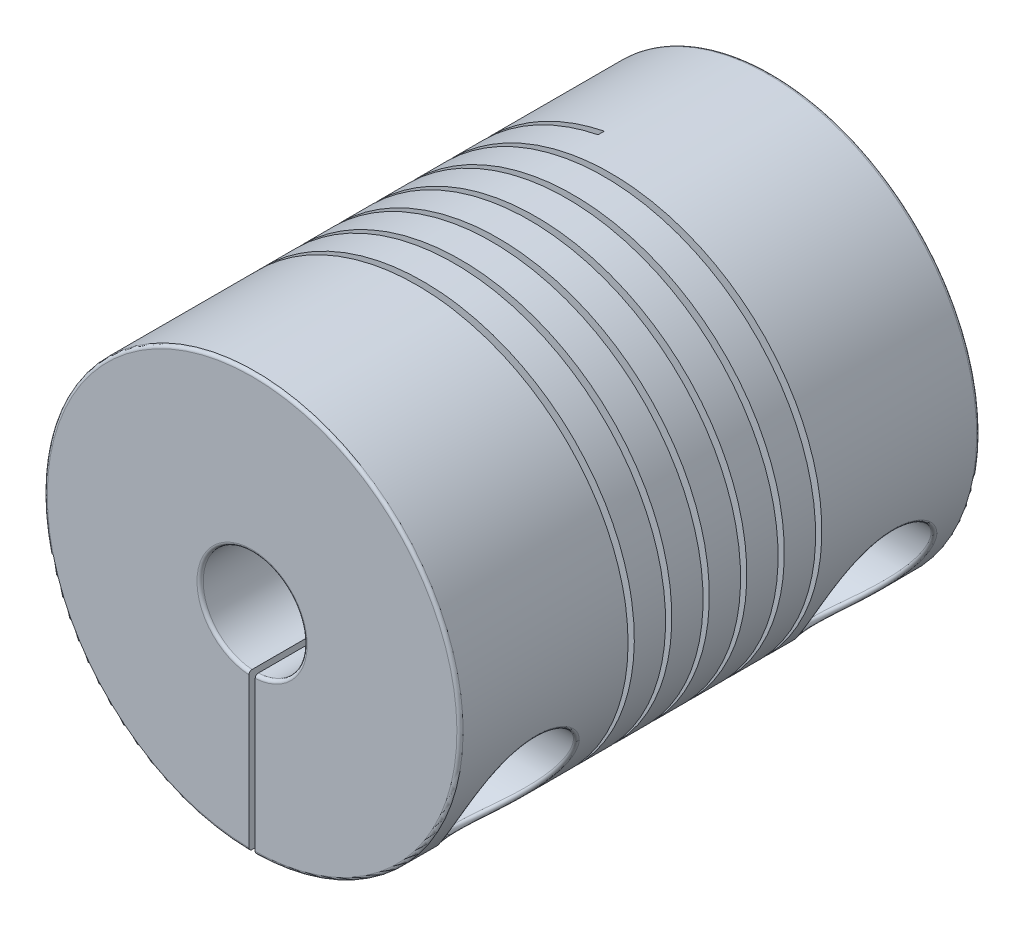
SolidWorks part; units mm, degrees
ref_plane "Front Plane" through (0, 0, 0) normal (0, 0, 1) x (1, 0, 0)
ref_plane "Top Plane" through (0, 0, 0) normal (0, 1, 0) x (1, 0, 0)
ref_plane "Right Plane" through (0, 0, 0) normal (1, 0, 0) x (0, 0, -1)
sketch "Sketch1" plane through (0, 0, 0) normal (0, 0, 1) x (1, 0, 0)
  circle A0 centre (0, 0) radius 10
  dimension "D1" = 20
extrude "Boss-Extrude1" add sketch "Sketch1" against normal blind 25
sketch "Sketch2" plane through (0, 0, 0) normal (0, 0, 1) x (1, 0, 0)
  circle A0 centre (0, 0) radius 2.5
  dimension "D1" = 5
extrude "Cut-Extrude1" cut sketch "Sketch2" against normal blind 12.5
sketch "Sketch3" plane through (0, 0, -25) normal (0, 0, -1) x (-1, 0, 0)
  circle A0 centre (0, 0) radius 2.5
  dimension "D1" = 5
extrude "Cut-Extrude2" cut sketch "Sketch3" against normal blind 12.5
ref_plane "Plane1" through (0, 0, -7.25) normal (0, 0, 1) x (1, 0, 0)
sketch "Sketch4" plane through (0, 0, -7.25) normal (0, 0, 1) x (1, 0, 0)
  circle A0 centre (0, 0) radius 11.25
  dimension "D1" = 22.5
curve "Helix/Spiral1" pitch 1.804 height 11.0044 turns 6.1
ref_plane "Plane2" through (-1.7599, 0, 0) normal (1, 0, 0) x (0, 0, -1)
sketch "Sketch5" plane through (-1.7599, 0, 0) normal (1, 0, 0) x (0, 0, -1)
  line L0 (15.0923, 11.41) -> (14.7923, 11.41)
  line L1 (14.7923, 11.41) -> (14.7923, 0)
  line L2 (14.7923, 0) -> (15.0923, 0)
  line L3 (15.0923, 0) -> (15.0923, 11.41)
  dimension "D1" = 11.41
  dimension "D3" = 0.3
sweep "Cut-Sweep2" cut profiles "Sketch5" path "Helix/Spiral1"
sketch "Sketch6" plane through (0, 0, 0) normal (0, 1, 0) x (1, 0, 0)
  line L0 (10, 25) -> (-10, 25) construction
  line L1 (-0.15, 0) -> (0.15, 0)
  line L2 (-0.15, 0) -> (-0.15, 25)
  line L3 (-0.15, 25) -> (0.15, 25)
  line L4 (0.15, 0) -> (0.15, 25)
  point P4 (0, 0)
  dimension "D1" = 0.3
extrude "Cut-Extrude3" cut sketch "Sketch6" against normal blind 12.5
ref_plane "Plane3" through (10, 0, 0) normal (1, 0, 0) x (0, 0, -1)
sketch "Sketch8" plane through (10, 0, 0) normal (1, 0, 0) x (0, 0, -1)
  line L0 (25, -9.9989) -> (25, 10) construction
  circle A0 centre (3.9, -5) radius 1.5
  circle A1 centre (21.1, -5) radius 1.5
  dimension "D1" = 3
  dimension "D2" = 5
  dimension "D3" = 3.9
  dimension "D4" = 3.9
extrude "Cut-Extrude4" cut sketch "Sketch8" against normal through all
sketch "Sketch10" plane through (10, 0, 0) normal (1, 0, 0) x (0, 0, -1)
  circle A2 centre (3.9, -5) radius 2.72
  circle A3 centre (3.9, -5) radius 2.72
  circle A12 centre (21.1, -5) radius 2.72
  circle A13 centre (21.1, -5) radius 2.72
  dimension "D1" = 1.22
  dimension "D2" = 1.22
extrude "Cut-Extrude6" cut sketch "Sketch10" against normal blind 6
fillet "Fillet1" radius 0.15 3 edges at (8.3976, -5.4295, -1.2141) (0, 2.5, 0) (0, 10, 0)
fillet "Fillet2" radius 0.15 3 edges at (0, 2.5, -25) (0, 10, -25) (8.3976, -5.4295, -18.4141)
